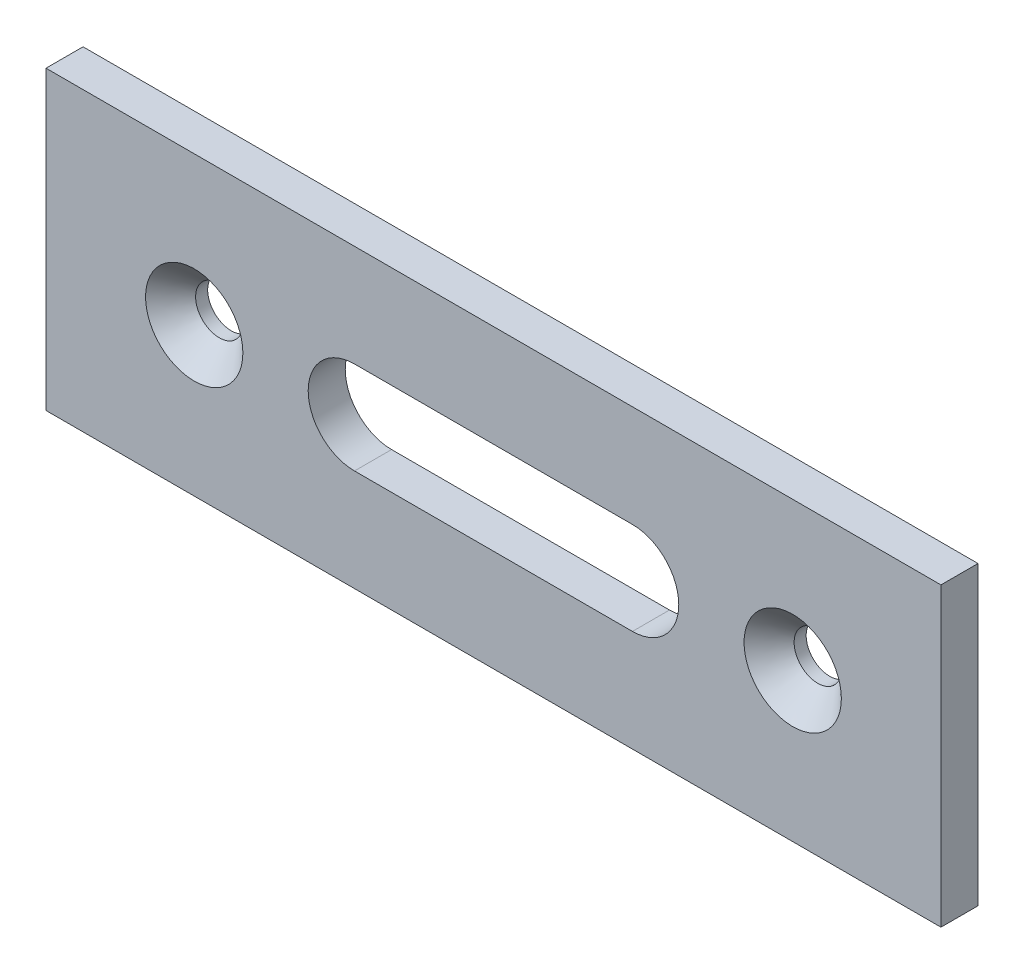
SolidWorks part; units mm, degrees
ref_plane "Plan de face" through (0, 0, 0) normal (0, 0, 1) x (1, 0, 0)
ref_plane "Plan de dessus" through (0, 0, 0) normal (0, 1, 0) x (1, 0, 0)
ref_plane "Plan de droite" through (0, 0, 0) normal (1, 0, 0) x (0, 0, -1)
sketch "Sketch1" plane through (0, 0, 0) normal (0, 0, 1) x (1, 0, 0)
  line L1 (-19.8825, 16.6713) -> (76.7175, 16.6713)
  line L2 (-19.8825, 16.6713) -> (-19.8825, -15.3287)
  line L3 (-19.8825, -15.3287) -> (76.7175, -15.3287)
  line L4 (76.7175, 16.6713) -> (76.7175, -15.3287)
  dimension "D1" = 32
  dimension "D2" = 96.6
extrude "Boss-Extrude1" add sketch "Sketch1" along normal blind 4
sketch "Sketch2" plane through (0, 0, 4) normal (0, 0, 1) x (1, 0, 0)
  line L0 (-19.8825, 16.6713) -> (-19.8825, -15.3287) construction
  line L1 (13.4175, 0.6713) -> (43.4175, 0.6713) construction
  line L2 (13.4175, 5.6713) -> (43.4175, 5.6713)
  line L4 (13.4175, -4.3287) -> (43.4175, -4.3287)
  line L5 (-19.8825, -15.3287) -> (76.7175, -15.3287) construction
  arc A3 (13.4175, 5.6713) -> (13.4175, -4.3287) centre (13.4175, 0.6713) ccw
  arc A4 (43.4175, -4.3287) -> (43.4175, 5.6713) centre (43.4175, 0.6713) ccw
  point P4 (28.4175, 0.6713)
  dimension "D1" = 48.3
  dimension "D4" = 16
  dimension "D2" = 10
  dimension "D3" = 30
extrude "Cut-Extrude1" cut sketch "Sketch2" against normal through all
sketch "Esquisse2" plane through (0, 0, 4) normal (0, 0, 1) x (1, 0, 0)
  line L0 (-19.8825, 16.6713) -> (-19.8825, -15.3287) construction
  line L1 (76.7175, -15.3287) -> (76.7175, 16.6713) construction
  line L2 (76.7175, 16.6713) -> (-19.8825, 16.6713) construction
  circle A0 centre (-3.8825, 0.6713) radius 5.25
  circle A1 centre (60.7175, 0.6713) radius 5.25
  dimension "D1" = 10.5
  dimension "D2" = 10.5
  dimension "D3" = 16
  dimension "D4" = 16
  dimension "D5" = 16
  dimension "D6" = 16
hole_wizard "Fraisage pour vis à tête fraisée bombée #51" positions "Esquisse3D1" profile "Esquisse3" countersink size "#5" standard "Ansi Inch" end condition through all
sketch3d "Esquisse3D1"
  point P0 (-3.8825, 0.6713, 4)
  point P3 (60.7175, 0.6713, 4)
sketch "Esquisse3" plane through (-3.8825, 0.6713, 4) normal (1, 0, 0) x (0, -1, 0)
  line L0 (0, 0) -> (0, 4)
  line L1 (0, 4) -> (2.55, 4)
  line L2 (2.55, 4) -> (2.55, 2.7)
  line L3 (2.55, 2.7) -> (5.25, 0)
  line L5 (5.25, 0) -> (0, 0)
  line L6 (-2.55, 2.7) -> (-5.25, 0) construction
  line L11 (0, -6.35) -> (0, 107.95) construction
  dimension "Diamètre du perçage jusqu'au prochain" = 5.1
  dimension "Profondeur du perçage jusqu'au prochain" = 4
  dimension "Diamètre du fraisage entrant" = 10.5
  dimension "Angle du fraisage entrant" = 90
